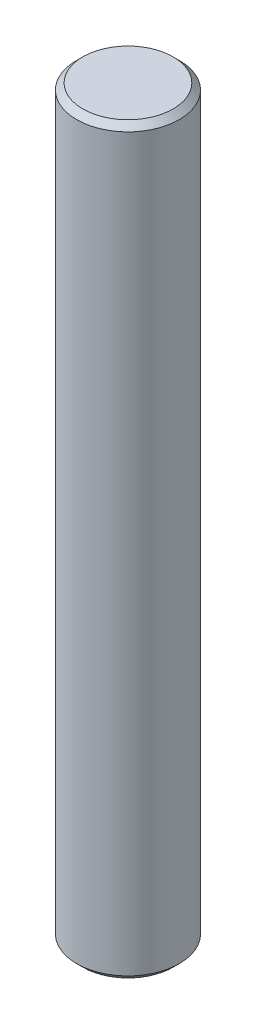
SolidWorks part; units mm, degrees
ref_plane "Front Plane" through (0, 0, 0) normal (0, 0, 1) x (1, 0, 0)
ref_plane "Top Plane" through (0, 0, 0) normal (0, 1, 0) x (1, 0, 0)
ref_plane "Right Plane" through (0, 0, 0) normal (1, 0, 0) x (0, 0, -1)
sketch "Sketch1" plane through (0, 0, 0) normal (0, 1, 0) x (1, 0, 0)
  circle A0 centre (0, 0) radius 2.5
  dimension "D1" = 5
extrude "Boss-Extrude1" add sketch "Sketch1" along normal blind 36.2
chamfer "Chamfer1" distance 0.3 angle 45 2 edges at (0, 0, 2.5) (0, 36.2, 2.5)
